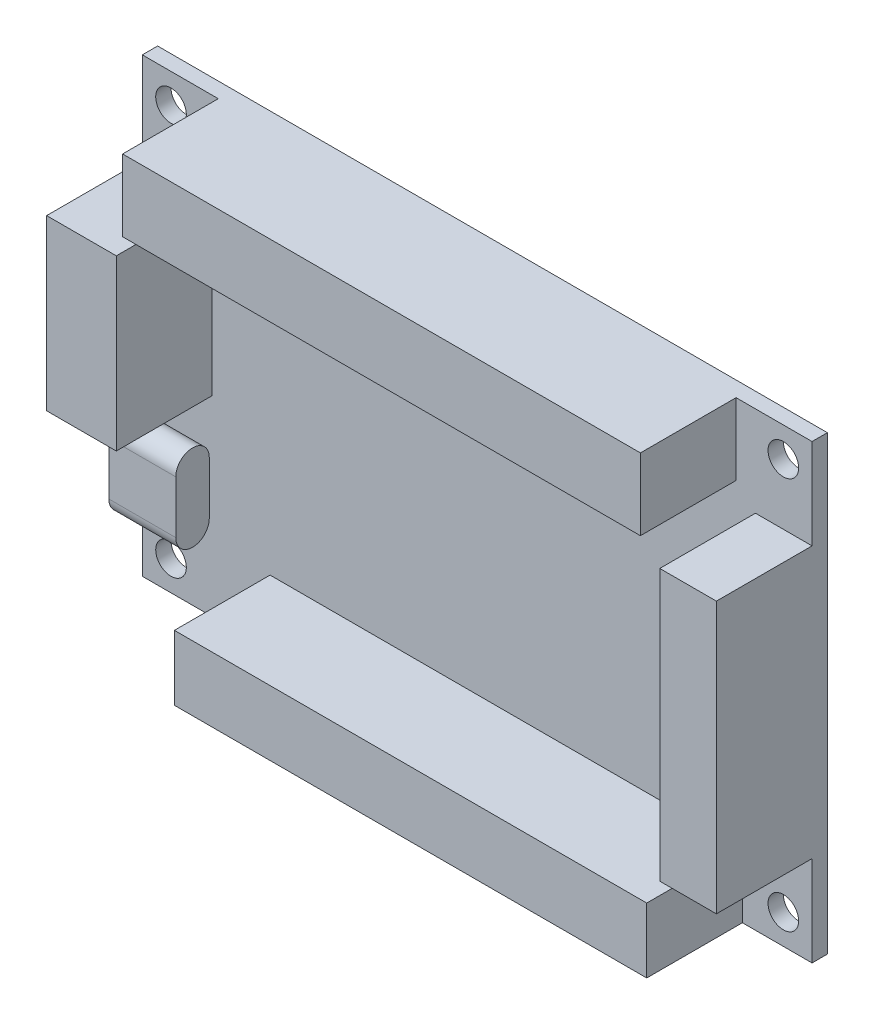
SolidWorks part; units mm, degrees
ref_plane "Plano frontal" through (0, 0, 0) normal (0, 0, 1) x (1, 0, 0)
ref_plane "Plano superior" through (0, 0, 0) normal (0, 1, 0) x (1, 0, 0)
ref_plane "Plano direito" through (0, 0, 0) normal (1, 0, 0) x (0, 0, -1)
sketch "Esboço1" plane through (0, 0, 0) normal (0, 0, 1) x (1, 0, 0)
  line L0 (-11.2515, 0) -> (0, 0) construction
  line L1 (-35, 23.6) -> (35, 23.6)
  line L2 (-35, 23.6) -> (-35, -23.6)
  line L3 (-35, -23.6) -> (35, -23.6)
  line L4 (35, 23.6) -> (35, -23.6)
  line L5 (-35, 23.6) -> (35, -23.6) construction
  line L6 (-35, -23.6) -> (35, 23.6) construction
  line L7 (0, 0) -> (0, 10.1302) construction
  circle A0 centre (-32, 20.5) radius 1.6
  circle A1 centre (32, 20.5) radius 1.6
  circle A2 centre (32, -20.5) radius 1.6
  circle A3 centre (-32, -20.5) radius 1.6
  point P0 (0, 0)
  dimension "D3" = 3.2
  dimension "D4" = 64
  dimension "D5" = 41
  dimension "D1" = 70
  dimension "D2" = 47.2
extrude "Ressalto-extrusão1" add sketch "Esboço1" along normal blind 1.6
sketch "Esboço2" plane through (0, 0, 1.6) normal (0, 0, 1) x (1, 0, 0)
  line L0 (35, 23.6) -> (-35, 23.6) construction
  line L5 (-35, -23.6) -> (35, -23.6) construction
  line L6 (-21.6463, -16.8142) -> (27.7202, -16.8142)
  line L7 (-27.0602, 16.1036) -> (27.0602, 16.1036)
  line L8 (-27.0602, 16.1036) -> (-27.0602, 23.6)
  line L9 (-27.0602, 23.6) -> (27.0602, 23.6)
  line L10 (27.0602, 16.1036) -> (27.0602, 23.6)
  line L11 (-27.0602, 16.1036) -> (27.0602, 23.6) construction
  line L12 (-27.0602, 23.6) -> (27.0602, 16.1036) construction
  line L13 (-21.6463, -16.8142) -> (-21.6463, -23.6)
  line L14 (-21.6463, -23.6) -> (27.7202, -23.6)
  line L15 (27.7202, -16.8142) -> (27.7202, -23.6)
  line L16 (-21.6463, -16.8142) -> (27.7202, -23.6) construction
  line L17 (-21.6463, -23.6) -> (27.7202, -16.8142) construction
  line L18 (35, -23.6) -> (35, 23.6) construction
  line L19 (29.0838, -14.1534) -> (35, -14.1534)
  line L20 (29.0838, -14.1534) -> (29.0838, 14.1534)
  line L21 (29.0838, 14.1534) -> (35, 14.1534)
  line L22 (35, -14.1534) -> (35, 14.1534)
  line L23 (29.0838, -14.1534) -> (35, 14.1534) construction
  line L24 (29.0838, 14.1534) -> (35, -14.1534) construction
  line L25 (-35, 23.6) -> (-35, -23.6) construction
  line L26 (-27.7202, -3.6213) -> (-35, -3.6213)
  line L27 (-27.7202, -3.6213) -> (-27.7202, 14.0487)
  line L28 (-27.7202, 14.0487) -> (-35, 14.0487)
  line L29 (-35, -3.6213) -> (-35, 14.0487)
  line L30 (-27.7202, -3.6213) -> (-35, 14.0487) construction
  line L31 (-27.7202, 14.0487) -> (-35, -3.6213) construction
  point P0 (3.037, -20.2071)
  point P5 (-27.5593, 14.0487)
  point P6 (0, 19.8518)
  point P15 (32.0419, 0)
  point P22 (-31.3601, 5.2137)
  point P29 (-27.7202, -3.6213)
  point P30 (-21.6463, -16.8142)
extrude "Ressalto-extrusão2" add sketch "Esboço2" along normal blind 10
sketch "Esboço3" plane through (-35, 0, 0) normal (-1, 0, 0) x (0, 0, 1)
  line L0 (3.35, -9.35) -> (3.35, -14.85) construction
  line L1 (5.1, -9.35) -> (5.1, -14.85)
  line L2 (1.6, -9.35) -> (1.6, -14.85)
  line L3 (1.6, -23.6) -> (0, -23.6) construction
  line L4 (1.6, -3.6213) -> (1.6, -23.6) construction
  arc A0 (5.1, -9.35) -> (1.6, -9.35) centre (3.35, -9.35) ccw
  arc A1 (1.6, -14.85) -> (5.1, -14.85) centre (3.35, -14.85) ccw
  point P2 (3.35, -12.1)
  point P9 (1.6, -9.1)
  dimension "D1" = 9
  dimension "D2" = 1.75
  dimension "D3" = 7
extrude "Ressalto-extrusão3" add sketch "Esboço3" against normal blind 7
